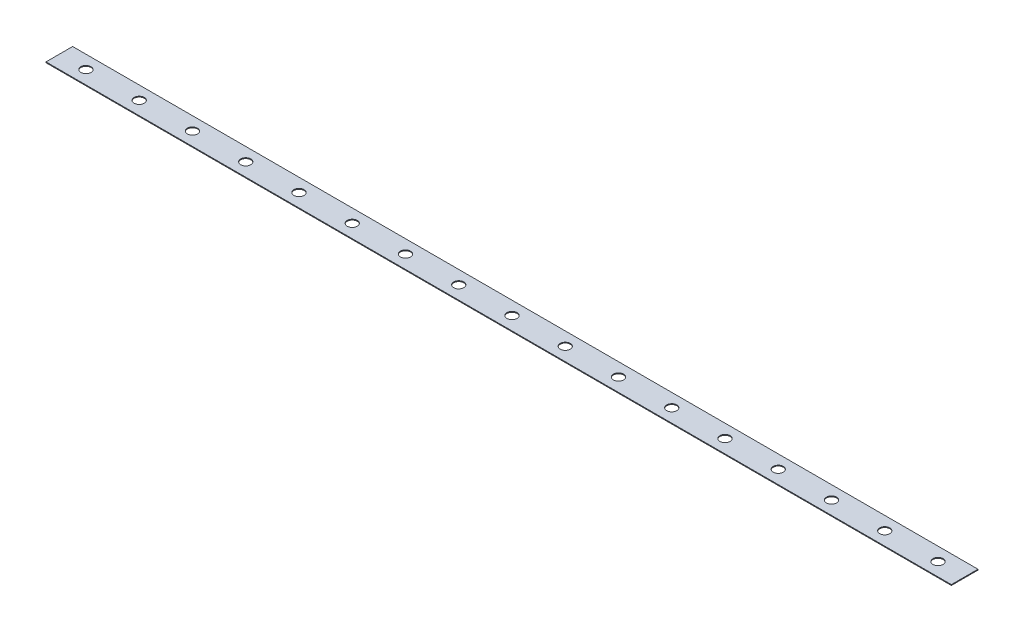
SolidWorks part; units mm, degrees
ref_plane "Front Plane" through (0, 0, 0) normal (0, 0, 1) x (1, 0, 0)
ref_plane "Top Plane" through (0, 0, 0) normal (0, 1, 0) x (1, 0, 0)
ref_plane "Right Plane" through (0, 0, 0) normal (1, 0, 0) x (0, 0, -1)
sketch "Sketch1" plane through (0, 0, 0) normal (0, 1, 0) x (1, 0, 0)
  line L1 (-215.9, 6.35) -> (215.9, 6.35)
  line L2 (-215.9, 6.35) -> (-215.9, -6.35)
  line L3 (-215.9, -6.35) -> (215.9, -6.35)
  line L4 (215.9, 6.35) -> (215.9, -6.35)
  line L5 (-215.9, 6.35) -> (215.9, -6.35) construction
  line L6 (-215.9, -6.35) -> (215.9, 6.35) construction
  point P0 (0, 0)
  dimension "D1" = 12.7
  dimension "D2" = 431.8
extrude "Boss-Extrude1" add sketch "Sketch1" along normal blind 0.381
sketch "Sketch2" plane through (0, 0.381, 0) normal (0, 1, 0) x (1, 0, 0)
  circle A0 centre (0, 0) radius 2.413
  circle A1 centre (-25.4, 0) radius 2.413
  circle A2 centre (25.4, 0) radius 2.413
  circle A3 centre (-50.8, 0) radius 2.413
  circle A4 centre (-76.2, 0) radius 2.413
  circle A5 centre (-101.6, 0) radius 2.413
  circle A6 centre (-127, 0) radius 2.413
  circle A7 centre (-152.4, 0) radius 2.413
  circle A8 centre (-177.8, 0) radius 2.413
  circle A9 centre (-203.2, 0) radius 2.413
  circle A10 centre (50.8, 0) radius 2.413
  circle A11 centre (76.2, 0) radius 2.413
  circle A12 centre (101.6, 0) radius 2.413
  circle A13 centre (127, 0) radius 2.413
  circle A14 centre (152.4, 0) radius 2.413
  circle A15 centre (177.8, 0) radius 2.413
  circle A16 centre (203.2, 0) radius 2.413
  dimension "D3" = 4.826
  dimension "D1" = 25.4
  dimension "D2" = 25.4
  dimension "D4" = 8
  dimension "D5" = 8
extrude "Cut-Extrude1" cut sketch "Sketch2" against normal through all
